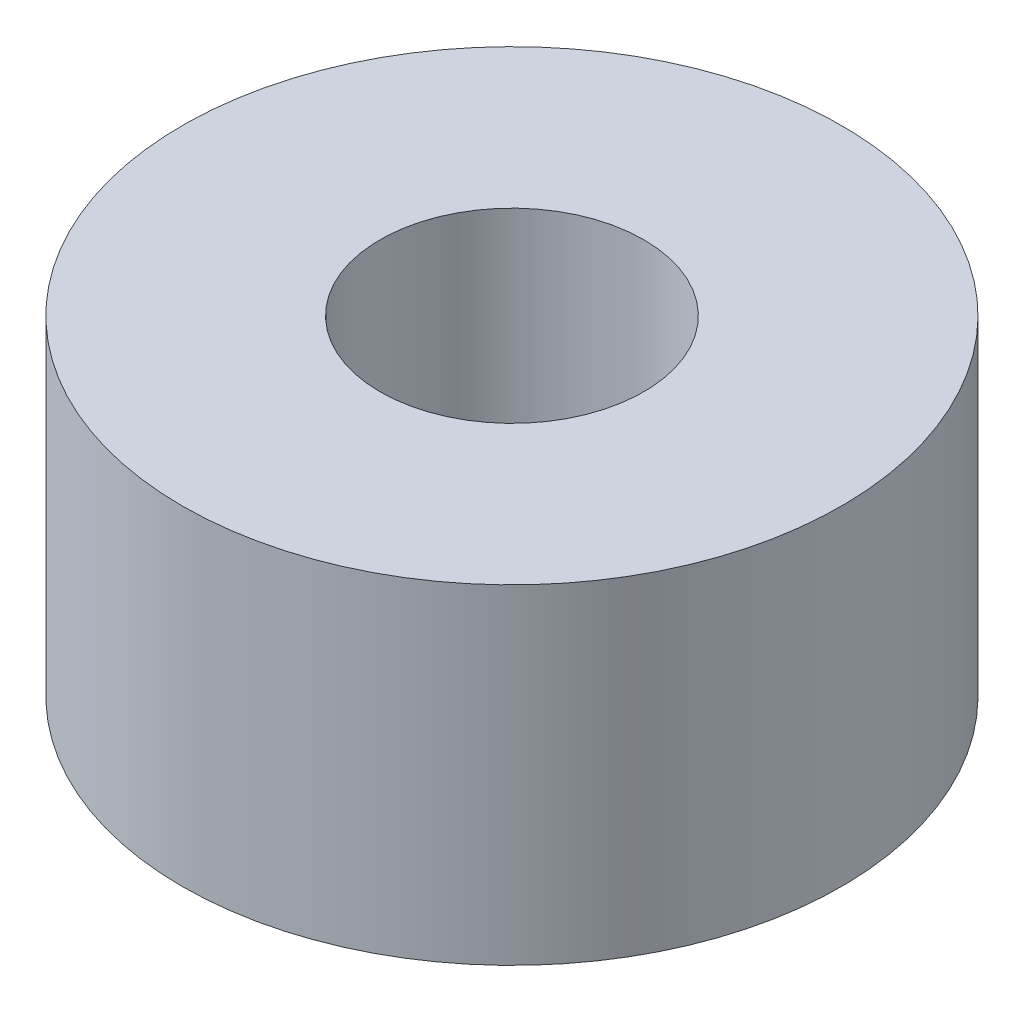
SolidWorks part; units mm, degrees
material "不锈钢 (铁素体)"
ref_plane "前视基准面" through (0, 0, 0) normal (0, 0, 1) x (1, 0, 0)
ref_plane "上视基准面" through (0, 0, 0) normal (0, 1, 0) x (1, 0, 0)
ref_plane "右视基准面" through (0, 0, 0) normal (1, 0, 0) x (0, 0, -1)
sketch "草图1" plane through (0, 0, 0) normal (0, 1, 0) x (1, 0, 0)
  circle A0 centre (0, 0) radius 1
  circle A1 centre (0, 0) radius 2.5
  dimension "D1" = 2
  dimension "D2" = 5
extrude "凸台-拉伸1" add sketch "草图1" along normal blind 2.5
